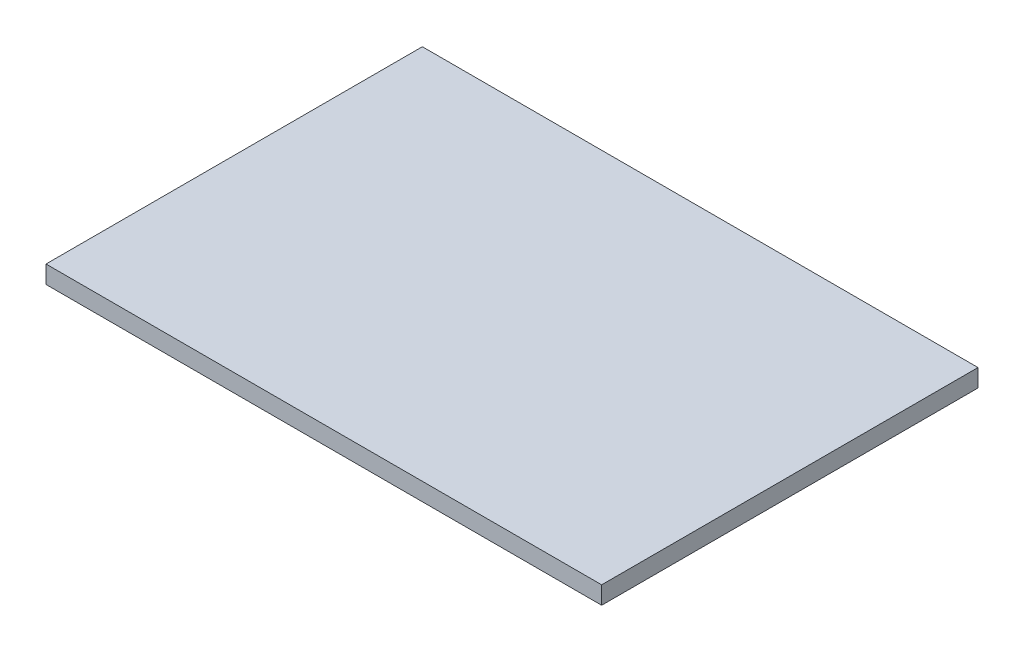
SolidWorks part; units mm, degrees
ref_plane "前视基准面" through (0, 0, 0) normal (0, 0, 1) x (1, 0, 0)
ref_plane "上视基准面" through (0, 0, 0) normal (0, 1, 0) x (1, 0, 0)
ref_plane "右视基准面" through (0, 0, 0) normal (1, 0, 0) x (0, 0, -1)
other "Configuration Table"
sketch "草图1" plane through (0, 0, 0) normal (0, 1, 0) x (1, 0, 0)
  line L1 (-141, 95.5) -> (141, 95.5)
  line L2 (-141, 95.5) -> (-141, -95.5)
  line L3 (-141, -95.5) -> (141, -95.5)
  line L4 (141, 95.5) -> (141, -95.5)
  line L5 (-141, 95.5) -> (141, -95.5) construction
  line L6 (-141, -95.5) -> (141, 95.5) construction
  point P0 (0, 0)
  dimension "D1" = 282
  dimension "D2" = 191
extrude "凸台-拉伸1" add sketch "草图1" along normal blind 9
